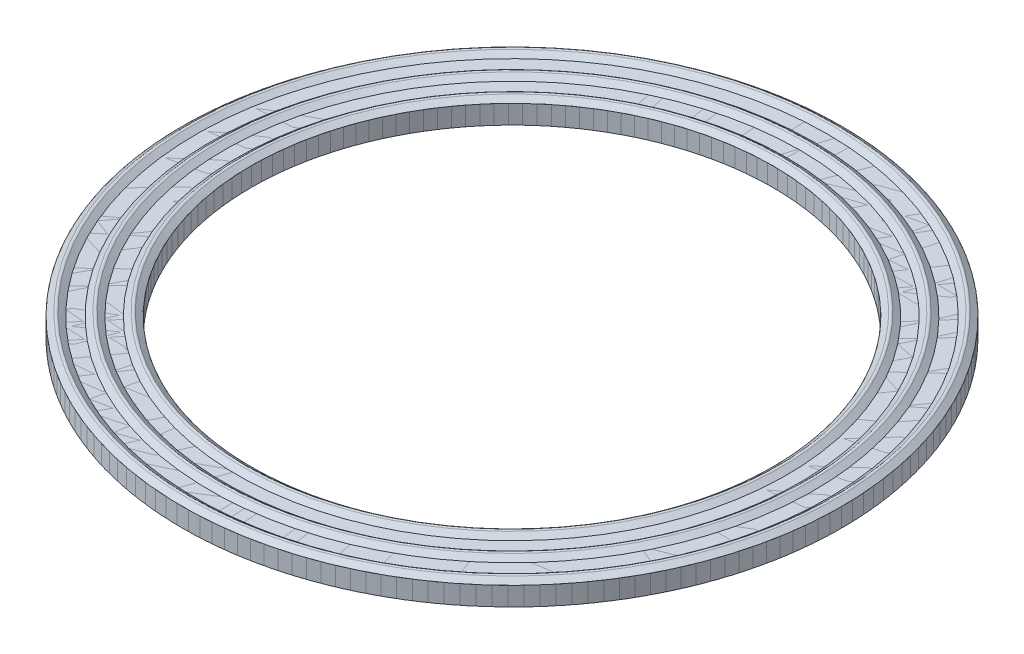
SolidWorks part; units mm, degrees
ref_plane "Front Plane" through (0, 0, 0) normal (0, 0, 1) x (1, 0, 0)
ref_plane "Top Plane" through (0, 0, 0) normal (0, 1, 0) x (1, 0, 0)
ref_plane "Right Plane" through (0, 0, 0) normal (1, 0, 0) x (0, 0, -1)
sketch "Sketch1" plane through (0, 0, 0) normal (0, 1, 0) x (1, 0, 0)
  line L0 (27.1716, 0) -> (34.3218, 0) construction
  circle A0 centre (0, 0) radius 27.1716
  circle A1 centre (0, 0) radius 34.3218
  dimension "D1" = 54.3433
  dimension "D2" = 7.1501
extrude "Boss-Extrude1" add sketch "Sketch1" along normal blind 1.9558
sketch "Sketch2" plane through (0, 0, 0) normal (1, 0, 0) x (0, 0, -1)
  line L0 (0, 0) -> (0, 24.3121) construction
  line L1 (0, 0) -> (0, -13.2945) construction
  line L2 (34.3218, 1.9558) -> (34.3218, 0)
  line L3 (34.3218, 0.9779) -> (-36.2396, 0.9779) construction
  line L4 (27.1716, 1.9558) -> (27.1716, 0)
  line L5 (27.1716, 0) -> (27.1716, 1.9558) construction
  line L6 (27.1716, 0) -> (27.1716, 1.9558) construction
  line L7 (27.1716, 1.9558) -> (27.745, 2.3923)
  line L8 (28.0527, 2.3923) -> (28.626, 1.9558)
  line L9 (34.3218, 1.9558) -> (33.7484, 2.3923)
  line L10 (33.4407, 2.3923) -> (32.8674, 1.9558)
  line L11 (29.9862, 1.9558) -> (30.5596, 2.3923)
  line L12 (30.8673, 2.3923) -> (31.4406, 1.9558)
  line L13 (28.626, 1.9558) -> (29.9862, 1.9558)
  line L14 (31.4406, 1.9558) -> (32.8674, 1.9558)
  line L15 (27.1716, 0) -> (28.4781, 0)
  line L16 (34.3218, 0) -> (32.9558, 0)
  line L17 (29.9937, 0) -> (31.4535, 0)
  line L18 (28.4781, 0) -> (29.1215, -0.3243)
  line L19 (29.3502, -0.3243) -> (29.9937, 0)
  line L20 (31.4535, 0) -> (32.0778, -0.3598)
  line L21 (32.3315, -0.3598) -> (32.9558, 0)
  arc A0 (29.1215, -0.3243) -> (29.3502, -0.3243) centre (29.2359, -0.0975) ccw
  arc A1 (32.0778, -0.3598) -> (32.3315, -0.3598) centre (32.2047, -0.1398) ccw
  arc A2 (33.7484, 2.3923) -> (33.4407, 2.3923) centre (33.5946, 2.1903) ccw
  arc A3 (30.8673, 2.3923) -> (30.5596, 2.3923) centre (30.7134, 2.1903) ccw
  arc A4 (28.0527, 2.3923) -> (27.745, 2.3923) centre (27.8988, 2.1903) ccw
  point P34 (29.2359, -0.3819)
  point P37 (32.2047, -0.433)
  point P40 (33.5946, 2.5095)
  point P43 (30.7134, 2.5095)
  point P46 (27.8988, 2.5095)
  dimension "D6" = 0.254
  dimension "D1" = 0.5537
  dimension "D2" = 0.914
  dimension "D3" = 2.8146
  dimension "D4" = 1.3064
  dimension "D5" = 1.3659
  dimension "D7" = 0.6435
  dimension "D8" = 0.6243
revolve "Revolve1" add sketch "Sketch2" angle 360 about L0
